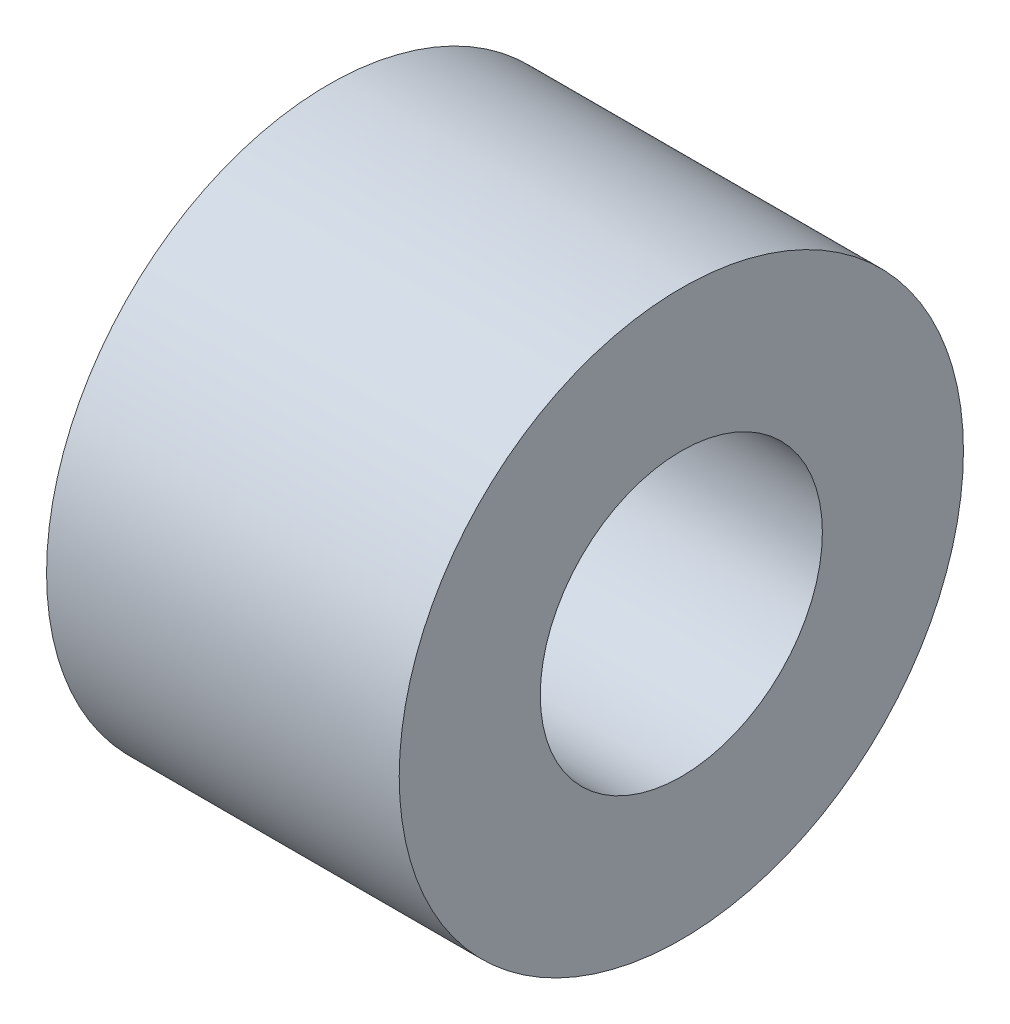
SolidWorks part; units mm, degrees
ref_plane "Front Plane" through (0, 0, 0) normal (0, 0, 1) x (1, 0, 0)
ref_plane "Top Plane" through (0, 0, 0) normal (0, 1, 0) x (1, 0, 0)
ref_plane "Right Plane" through (0, 0, 0) normal (1, 0, 0) x (0, 0, -1)
sketch "Sketch1" plane through (0, 0, 0) normal (0, 0, 1) x (1, 0, 0)
  line L0 (0, 0) -> (5, 0) construction
  line L1 (0, -2) -> (5, -2)
  line L2 (5, -2) -> (5, -4)
  line L3 (5, -4) -> (0, -4)
  line L4 (0, -4) -> (0, -2)
  dimension "D1" = 5
  dimension "D2" = 2
  dimension "D3" = 4
revolve "Revolve1" add sketch "Sketch1" angle 360 about L0
